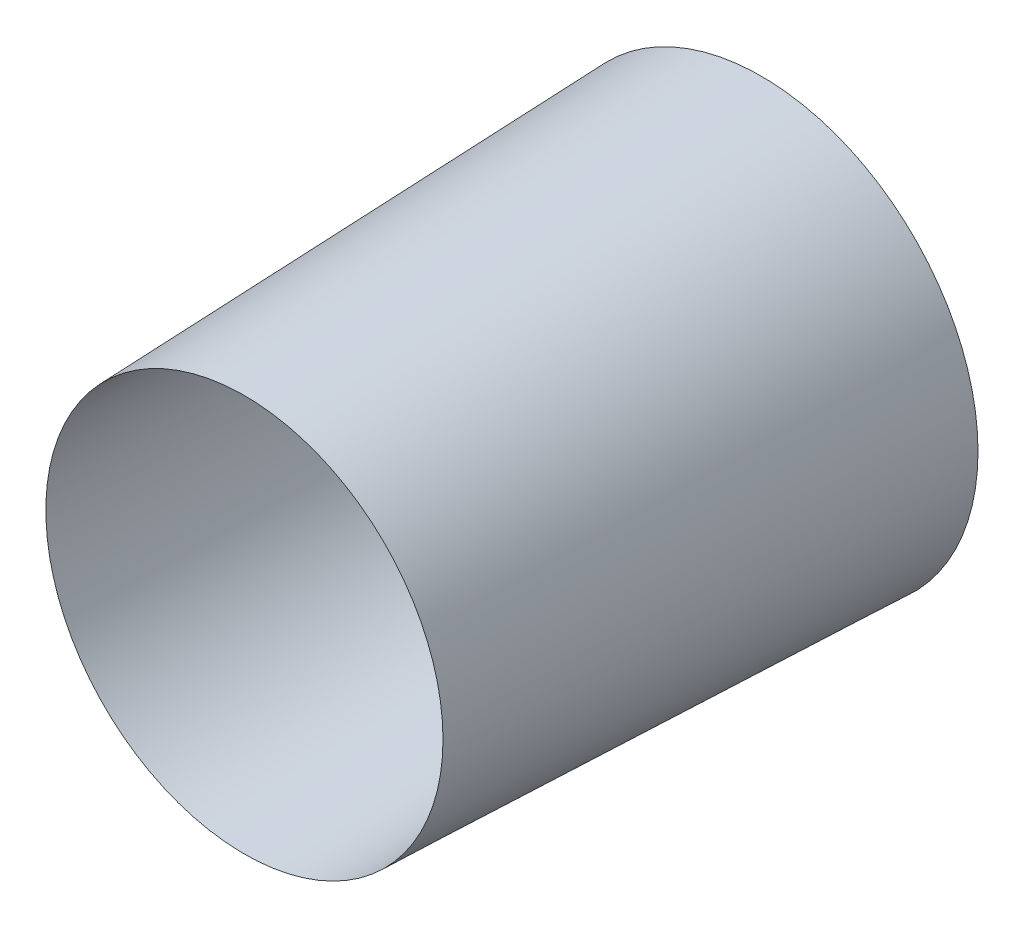
SolidWorks part; units mm, degrees
ref_plane "Front Plane" through (0, 0, 0) normal (0, 0, 1) x (1, 0, 0)
ref_plane "Top Plane" through (0, 0, 0) normal (0, 1, 0) x (1, 0, 0)
ref_plane "Right Plane" through (0, 0, 0) normal (1, 0, 0) x (0, 0, -1)
sketch "Sketch2" plane through (0, 0, 0) normal (0, 0, 1) x (1, 0, 0)
  circle A0 centre (0, 0) radius 10
  dimension "D1" = 20
extrude "Extrude-Thin1" add sketch "Sketch2" along normal blind 30 draft 2 thin
